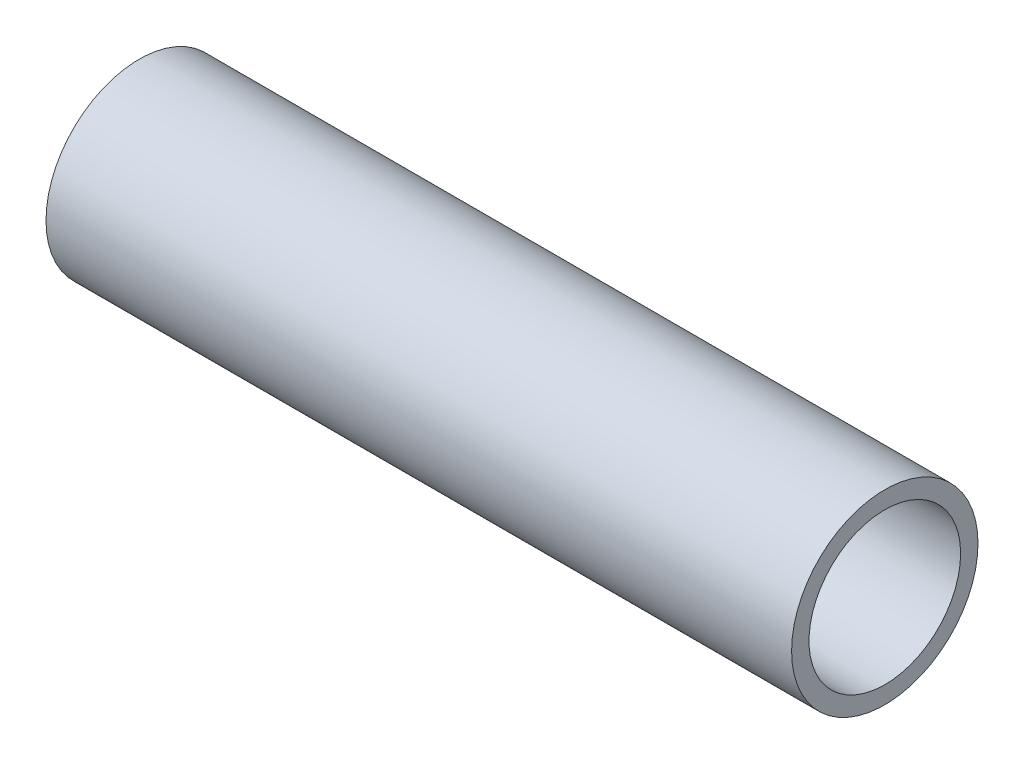
SolidWorks part; units mm, degrees
material "AISI 316 Stainless Steel Sheet (SS)"
ref_plane "Front" through (0, 0, 0) normal (0, 0, 1) x (1, 0, 0)
ref_plane "Top" through (0, 0, 0) normal (0, 1, 0) x (1, 0, 0)
ref_plane "Right" through (0, 0, 0) normal (1, 0, 0) x (0, 0, -1)
sketch "Sketch1" plane through (0, 0, 0) normal (1, 0, 0) x (0, 0, -1)
  circle A0 centre (0, 0) radius 4.7625
  circle A1 centre (0, 0) radius 3.8735
  point P4 (4.7625, 0)
  point P5 (3.8735, 0)
  dimension "OD" = 9.525
  dimension "ID" = 7.747
  dimension "Wall" = 0.889
extrude "Extrude1" add sketch "Sketch1" along normal mid plane 38.1
sketch "Sketch2" plane through (0, 0, 0) normal (0, 0, 1) x (1, 0, 0)
  line L0 (-19.05, 0) -> (19.05, 0) construction
  line L1 (-19.05, 4.7625) -> (-19.05, -4.7625) construction
